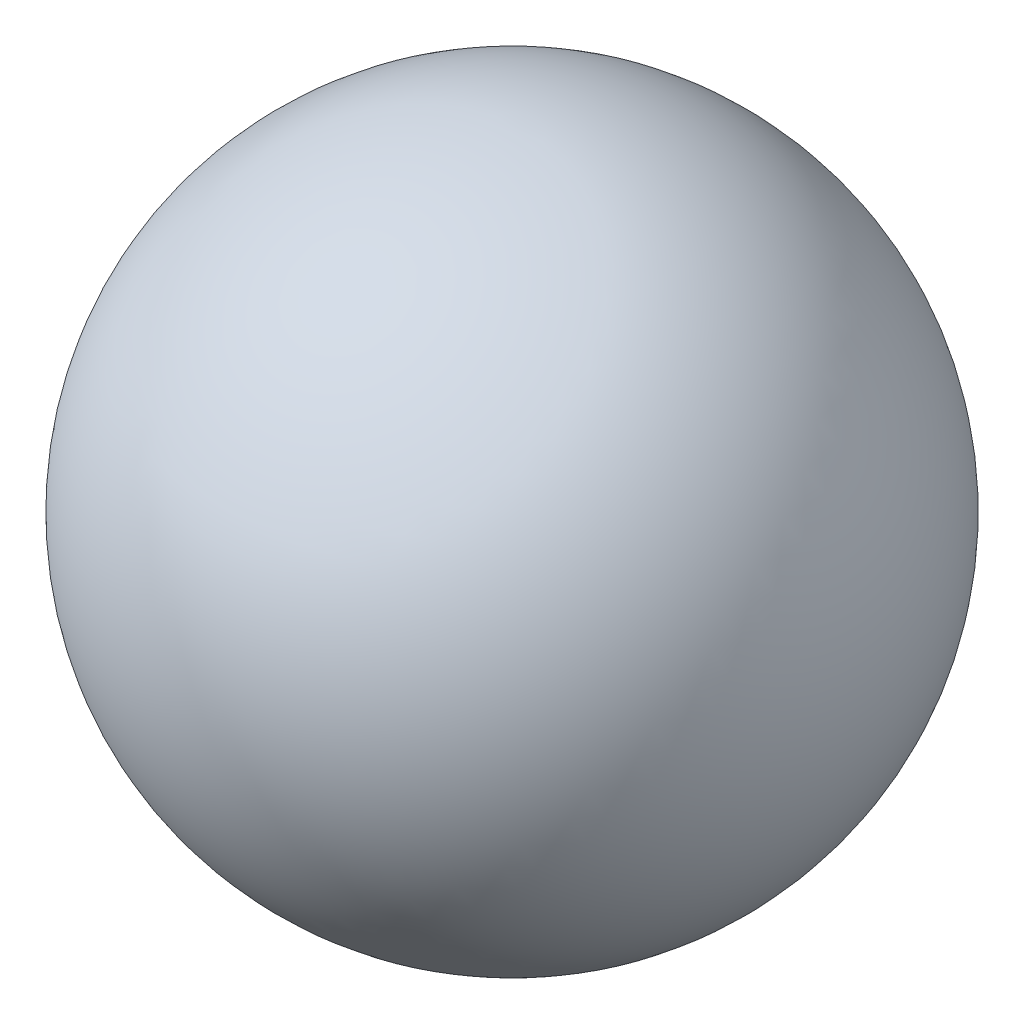
SolidWorks part; units mm, degrees
ref_plane "Plan de face" through (0, 0, 0) normal (0, 0, 1) x (1, 0, 0)
ref_plane "Plan de dessus" through (0, 0, 0) normal (0, 1, 0) x (1, 0, 0)
ref_plane "Plan de droite" through (0, 0, 0) normal (1, 0, 0) x (0, 0, -1)
sketch "Esquisse1" plane through (0, 0, 0) normal (0, 0, 1) x (1, 0, 0)
  line L1 (0, 12) -> (0, -12)
  arc A0 (0, 12) -> (0, -12) centre (0, 0) ccw
  point P1 (-12, 0)
  dimension "D1" = 12
  dimension "D2" = 24
revolve "Révolution4" add sketch "Esquisse1" angle 360 about L1
